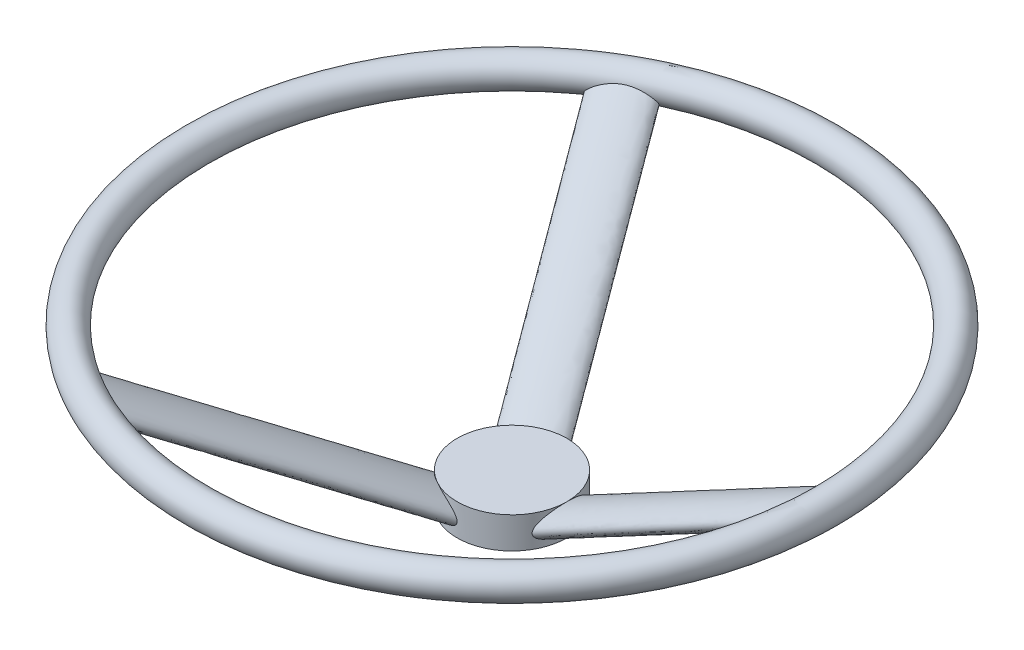
SolidWorks part; units mm, degrees
ref_plane "Front Plane" through (0, 0, 0) normal (0, 0, 1) x (1, 0, 0)
ref_plane "Top Plane" through (0, 0, 0) normal (0, 1, 0) x (1, 0, 0)
ref_plane "Right Plane" through (0, 0, 0) normal (1, 0, 0) x (0, 0, -1)
sketch "Sketch1" plane through (0, 0, 0) normal (0, 0, 1) x (1, 0, 0)
  line L1 (0, 0) -> (35, 0)
  line L2 (0, 0) -> (0, 20)
  line L3 (0, 20) -> (35, 20)
  line L4 (35, 0) -> (35, 20)
  circle A0 centre (200, 100) radius 10
  dimension "D3" = 20
  dimension "D1" = 35
  dimension "D2" = 20
  dimension "D4" = 100
  dimension "D5" = 200
revolve "Revolve1" add sketch "Sketch1" angle 360 about L2
sketch "Sketch2" plane through (0, 0, 0) normal (0, 0, 1) x (1, 0, 0)
  line L0 (35, 12) -> (200, 100)
  line L2 (35, 0) -> (35, 20) construction
  arc A0 (200, 90) -> (200, 110) centre (200, 100) ccw construction
  point P4 (0, 0)
  dimension "D1" = 8
ref_plane "Plane1" through (200, 100, 0) normal (0.8824, 0.4706, 0) x (0, 0, -1)
sketch "Sketch3" plane through (200, 100, 0) normal (0.8824, 0.4706, 0) x (0, 0, -1)
  ellipse E0 centre (0, -0.4275) end of major axis (17.5, -0.4275) minor radius 7.5
  dimension "D1" = 35
  dimension "D2" = 15
extrude "Boss-Extrude1" add sketch "Sketch3" against normal up to surface (192.5423 mm away)
pattern_circular "CirPattern1" count 3 over 360 about axis through (0, 0, 0) along (0, -1, 0) of "Boss-Extrude1"
